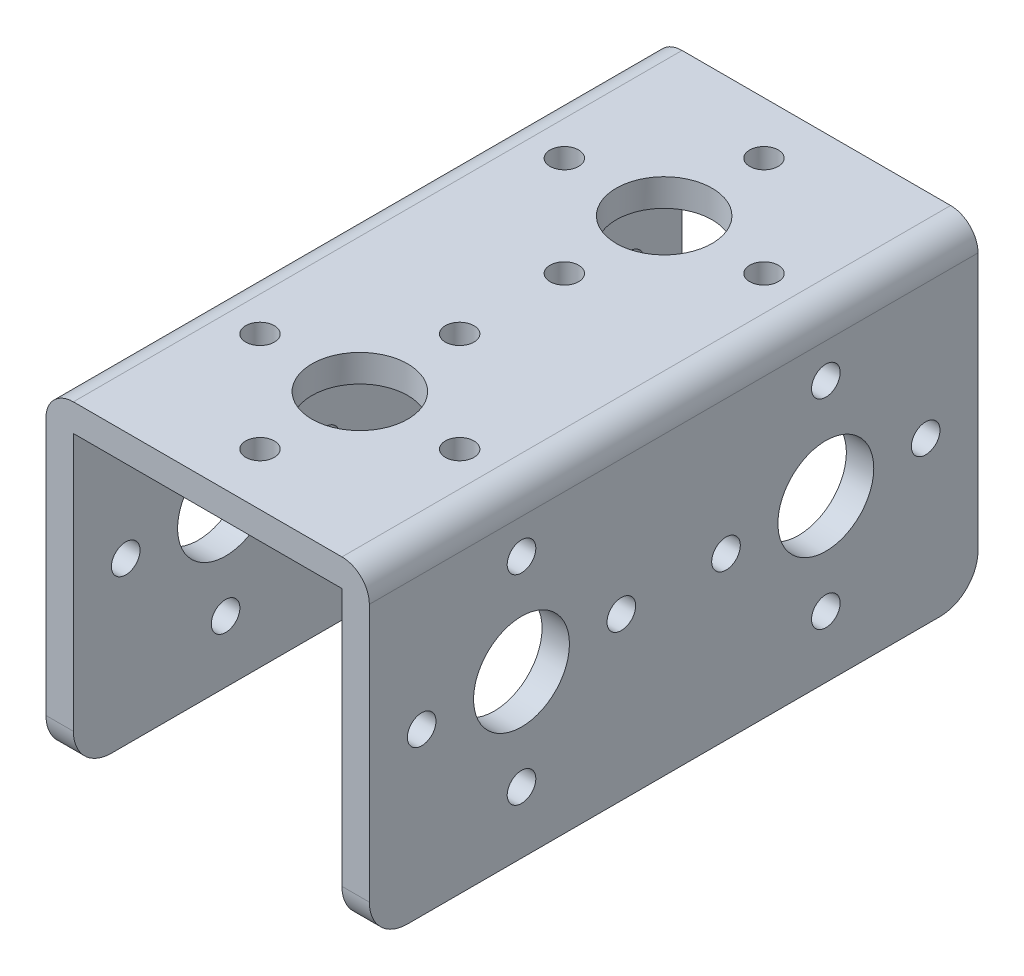
SolidWorks part; units mm, degrees
material "Alloy Steel"
ref_plane "Front Plane" through (0, 0, 0) normal (0, 0, 1) x (1, 0, 0)
ref_plane "Top Plane" through (0, 0, 0) normal (0, 1, 0) x (1, 0, 0)
ref_plane "Right Plane" through (0, 0, 0) normal (1, 0, 0) x (0, 0, -1)
sketch "Sketch1" plane through (0, 0, 0) normal (0, 0, 1) x (1, 0, 0)
  line L1 (11.2077, -26.9875) -> (11.2077, -2.286)
  line L2 (-13.4937, -26.9875) -> (-11.2077, -26.9875)
  line L3 (-13.4937, -26.9875) -> (-13.4937, 0)
  line L4 (-13.4937, 0) -> (13.4937, 0)
  line L5 (13.4937, -26.9875) -> (13.4937, 0)
  line L6 (-11.2077, -2.286) -> (11.2077, -2.286)
  line L7 (-11.2077, -26.9875) -> (-11.2077, -2.286)
  line L8 (11.2077, -26.9875) -> (13.4937, -26.9875)
  dimension "D1" = 26.9875
  dimension "D2" = 26.9875
  dimension "D3" = 2.286
extrude "Extrude1" add sketch "Sketch1" against normal blind 50.8
sketch "Sketch2" plane through (13.4937, -15.2925, -16.4098) normal (1, 0, 0) x (0, 0, -1)
  line L0 (34.3902, -11.695) -> (-16.4098, -11.695) construction
  line L1 (-3.7098, 10.1236) -> (-3.7098, 1.7924) construction
  line L2 (-16.4098, -11.695) -> (-16.4098, 15.2925) construction
  circle A0 centre (-3.7098, 1.7924) radius 4.0005
  circle A1 centre (-3.7098, 10.1236) radius 1.1938
  circle A2 centre (-3.7098, 1.7924) radius 8.3312 construction
  circle A3 centre (4.6214, 1.7924) radius 1.1938
  circle A4 centre (-3.7098, -6.5388) radius 1.1938
  circle A5 centre (-12.041, 1.7924) radius 1.1938
  dimension "D1" = 8.001
  dimension "D2" = 16.6624
  dimension "D3" = 2.3876
  dimension "D5" = 12.7
  dimension "D4" = 13.4874
extrude "Cut-Extrude1" cut sketch "Sketch2" against normal through all
other "ServoHornMtg<1>"
sketch "Sketch22" plane through (-3.6403, 0, -15.2607) normal (0, 1, 0) x (-1, 0, 0)
  line L0 (-14.8481, 2.5607) -> (-17.1341, 2.5607) construction
  line L1 (-3.6403, 10.8919) -> (-3.6403, 2.5607) construction
  circle A0 centre (-3.6403, 2.5607) radius 4.0005
  circle A1 centre (-3.6403, 10.8919) radius 1.1938
  circle A2 centre (-3.6403, 2.5607) radius 8.3312 construction
  circle A3 centre (4.6909, 2.5607) radius 1.1938
  circle A4 centre (-3.6403, -5.7705) radius 1.1938
  circle A5 centre (-11.9715, 2.5607) radius 1.1938
  dimension "D1" = 8.001
  dimension "D2" = 16.6624
  dimension "D3" = 2.3876
extrude "Cut-Extrude12" cut sketch "Sketch22" against normal through all
other "ServoHornMtg<3>"
pattern_linear "LPattern1" count 2 spacing 25.4 along (0, 0, -1) of "Cut-Extrude1", "Cut-Extrude12"
fillet "Fillet1" radius 2.286 2 edges at (13.4937, 0, -25.4) (-13.4937, 0, -25.4)
fillet "Fillet2" radius 3.175 4 edges at (12.3507, -26.9875, -50.8) (-12.3507, -26.9875, -50.8) (-12.3507, -26.9875, 0) (12.3507, -26.9875, 0)
